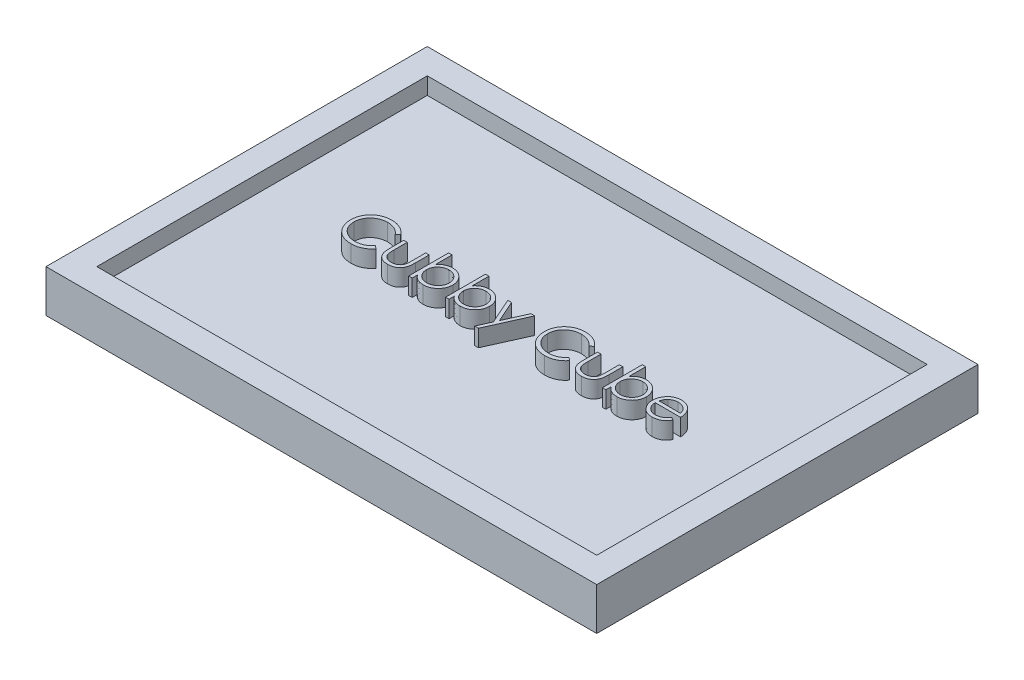
SolidWorks part; units mm, degrees
ref_plane "Front Plane" through (0, 0, 0) normal (0, 0, 1) x (1, 0, 0)
ref_plane "Top Plane" through (0, 0, 0) normal (0, 1, 0) x (1, 0, 0)
ref_plane "Right Plane" through (0, 0, 0) normal (1, 0, 0) x (0, 0, -1)
sketch "Sketch1" plane through (0, 0, 0) normal (0, 1, 0) x (1, 0, 0)
  line L1 (0, 0) -> (82.55, 0)
  line L2 (0, 0) -> (0, 57.15)
  line L3 (0, 57.15) -> (82.55, 57.15)
  line L4 (82.55, 0) -> (82.55, 57.15)
  dimension "D1" = 82.55
  dimension "D2" = 57.15
extrude "Boss-Extrude1" add sketch "Sketch1" along normal blind 6.35
shell "Shell1" thickness 3.81
sketch "Sketch2" plane through (0, 3.81, 0) normal (0, 1, 0) x (1, 0, 0)
  text T0 "Cubby Cube" font "Century Gothic" height in points 22
extrude "Boss-Extrude2" add sketch "Sketch2" along normal blind 2.54
